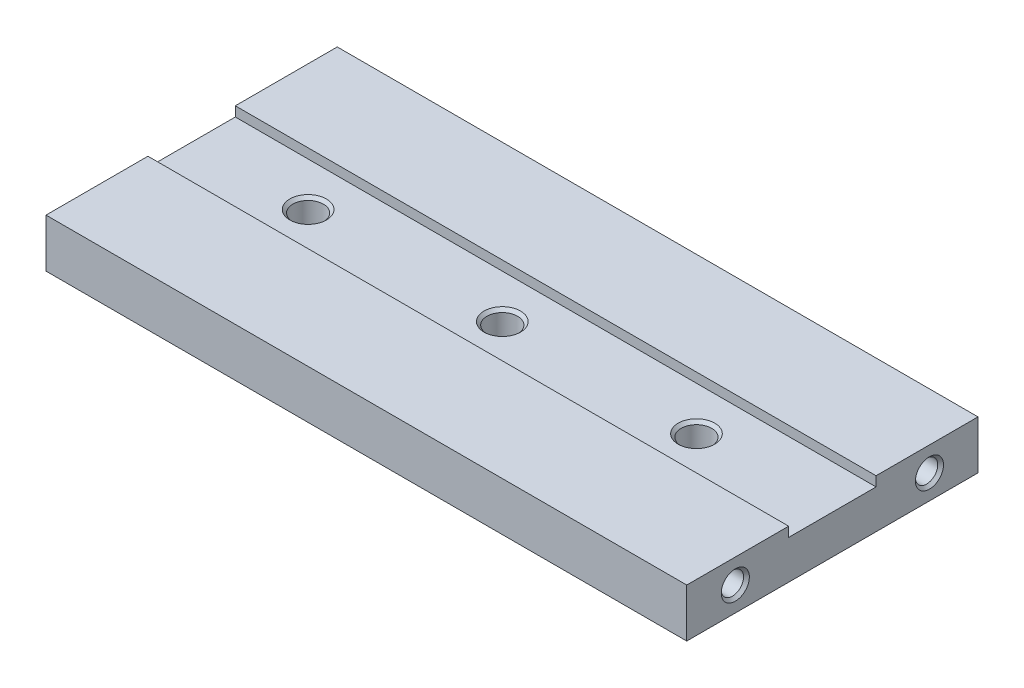
SolidWorks part; units mm, degrees
material "Liga 6061"
ref_plane "Plano frontal" through (0, 0, 0) normal (0, 0, 1) x (1, 0, 0)
ref_plane "Plano superior" through (0, 0, 0) normal (0, 1, 0) x (1, 0, 0)
ref_plane "Plano direito" through (0, 0, 0) normal (1, 0, 0) x (0, 0, -1)
sketch "Esboço1" plane through (0, 0, 0) normal (0, 1, 0) x (1, 0, 0)
  line L1 (33, -15) -> (-33, -15)
  line L2 (33, -15) -> (33, 15)
  line L3 (33, 15) -> (-33, 15)
  line L4 (-33, -15) -> (-33, 15)
  line L5 (33, -15) -> (-33, 15) construction
  line L6 (33, 15) -> (-33, -15) construction
  point P0 (0, 0)
  dimension "D1" = 66
  dimension "D2" = 30
extrude "Ressalto-extrusão1" add sketch "Esboço1" along normal blind 5
sketch "Esboço2" plane through (0, 5, 0) normal (0, 1, 0) x (1, 0, 0)
  line L0 (-33, 15) -> (-33, -15) construction
  line L1 (33, -4.5) -> (-33, -4.5)
  line L2 (33, -4.5) -> (33, 4.5)
  line L3 (33, 4.5) -> (-33, 4.5)
  line L4 (-33, -4.5) -> (-33, 4.5)
  line L5 (33, -4.5) -> (-33, 4.5) construction
  line L6 (33, 4.5) -> (-33, -4.5) construction
  point P0 (0, 0)
  dimension "D1" = 9
extrude "Corte-extrusão1" cut sketch "Esboço2" against normal blind 1
hole_wizard "Furo roscado para conduíte de M2.2x0.451" positions "Esboço5" profile "Esboço4" tap size "M2.2x0.45" standard "Helicoil® Metric"
sketch "Esboço5" plane through (33, 0, 0) normal (1, 0, 0) x (0, 0, -1)
  line L0 (-15, 5) -> (-15, 0) construction
  line L1 (-15, 5) -> (-4.5, 5) construction
  line L2 (4.5, 5) -> (15, 5) construction
  line L3 (15, 5) -> (15, 0) construction
  point P0 (-10, 2.5)
  point P2 (10, 2.5)
  dimension "D1" = 5
  dimension "D2" = 2.5
  dimension "D3" = 2.5
  dimension "D4" = 5
sketch "Esboço4" plane through (33, 2.5, 10) normal (0, 1, 0) x (0, 0, -1)
  line L0 (0, 0) -> (0, 6.691)
  line L1 (0, 6.691) -> (1.15, 6)
  line L2 (1.15, 6) -> (1.15, 0.2975)
  line L3 (1.15, 0.2975) -> (1.4475, 0)
  line L5 (1.4475, 0) -> (0, 0)
  line L6 (-1.15, 0.2975) -> (-1.4475, 0) construction
  line L10 (0, 6.691) -> (-1.15, 6) construction
  line L11 (0, -6.35) -> (0, 107.95) construction
  dimension "Tap Drill Dia." = 2.3
  dimension "Tap Drill Depth" = 6
  dimension "Near C'Sink Dia." = 2.895
  dimension "Near C'Sink Angle" = 90
  dimension "Drill Angle" = 118
cosmetic thread "Rosca de furo1" parameters "D1"=2.7, "D2"=2.845
cosmetic thread "Rosca de furo2" parameters "D1"=2.7, "D2"=2.845
hole_wizard "Furo roscado para conduíte de M2.2x0.452" positions "Esboço6" profile "Esboço7" tap size "M2.2x0.45" standard "Helicoil® Metric"
sketch "Esboço6" plane through (-33, 0, 0) normal (-1, 0, 0) x (0, 0, 1)
  line L0 (-15, 5) -> (-15, 0) construction
  line L1 (-15, 0) -> (15, 0) construction
  line L2 (15, 5) -> (15, 0) construction
  point P0 (-10, 2.5)
  point P2 (10, 2.5)
  dimension "D1" = 5
  dimension "D2" = 2.5
  dimension "D3" = 2.5
  dimension "D4" = 5
sketch "Esboço7" plane through (-33, 2.5, -10) normal (0, 1, 0) x (0, 0, 1)
  line L0 (0, 0) -> (0, 6.691)
  line L1 (0, 6.691) -> (1.15, 6)
  line L2 (1.15, 6) -> (1.15, 0.2975)
  line L3 (1.15, 0.2975) -> (1.4475, 0)
  line L5 (1.4475, 0) -> (0, 0)
  line L6 (-1.15, 0.2975) -> (-1.4475, 0) construction
  line L10 (0, 6.691) -> (-1.15, 6) construction
  line L11 (0, -6.35) -> (0, 107.95) construction
  dimension "Tap Drill Dia." = 2.3
  dimension "Tap Drill Depth" = 6
  dimension "Near C'Sink Dia." = 2.895
  dimension "Near C'Sink Angle" = 90
  dimension "Drill Angle" = 118
cosmetic thread "Rosca de furo3"
cosmetic thread "Rosca de furo4"
hole_wizard "Furo roscado para conduíte de M3x0.53" positions "Esboço8" profile "Esboço9" tap size "M3x0.5" standard "Helicoil® Metric" end condition through all
sketch "Esboço8" plane through (0, 4, 0) normal (0, 1, 0) x (1, 0, 0)
  line L0 (-33, 4.5) -> (-33, -4.5) construction
  point P0 (-21, 0)
  point P2 (-1, 0)
  point P4 (19, 0)
  dimension "D1" = 12
  dimension "D2" = 20
  dimension "D3" = 20
sketch "Esboço9" plane through (-21, 4, 0) normal (1, 0, 0) x (0, 0, 1)
  line L0 (0, 0) -> (0, 4)
  line L1 (0, 4) -> (1.575, 4)
  line L2 (1.575, 4) -> (1.575, 0.308)
  line L3 (1.575, 0.308) -> (1.883, 0)
  line L5 (1.883, 0) -> (0, 0)
  line L6 (-1.575, 0.308) -> (-1.883, 0) construction
  line L11 (0, -6.35) -> (0, 107.95) construction
  dimension "Thru Tap Drill Dia." = 3.15
  dimension "Thru Tap Drill Depth" = 4
  dimension "Near C'Sink Dia." = 3.766
  dimension "Near C'Sink Angle" = 90
cosmetic thread "Rosca de furo5"
cosmetic thread "Rosca de furo6"
cosmetic thread "Rosca de furo7"
